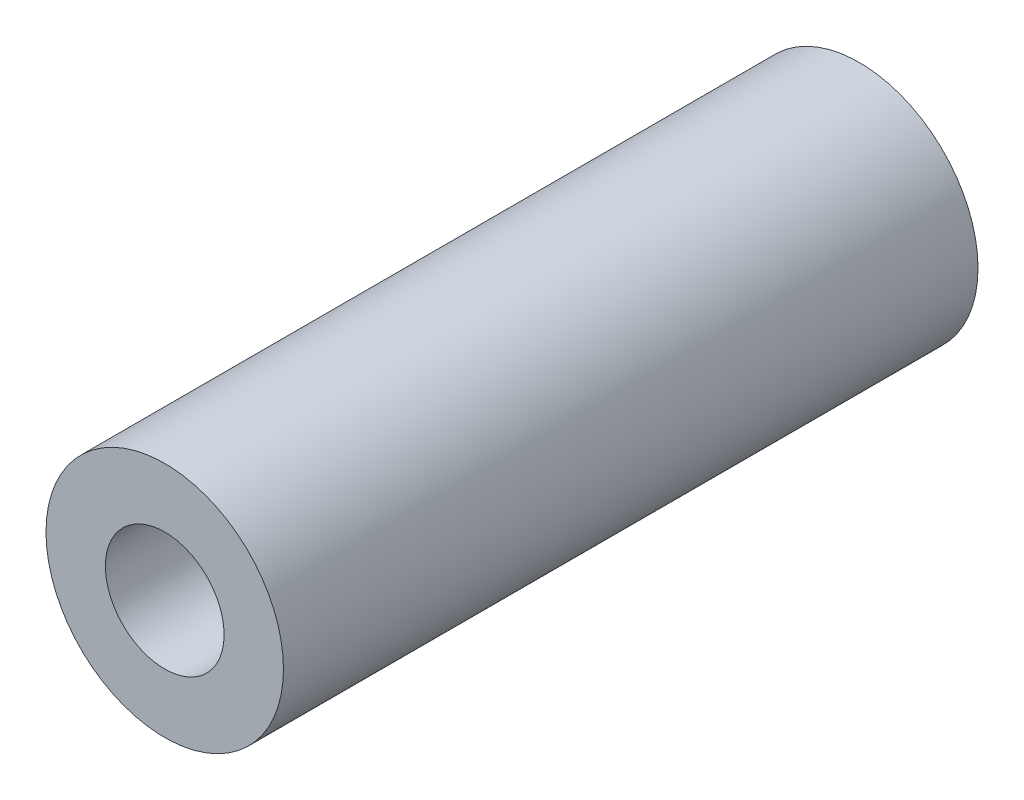
SolidWorks part; units mm, degrees
ref_plane "Alzado" through (0, 0, 0) normal (0, 0, 1) x (1, 0, 0)
ref_plane "Planta" through (0, 0, 0) normal (0, 1, 0) x (1, 0, 0)
ref_plane "Vista lateral" through (0, 0, 0) normal (1, 0, 0) x (0, 0, -1)
sketch "Croquis1" plane through (0, 0, 0) normal (0, 0, 1) x (1, 0, 0)
  circle A0 centre (0, 0) radius 1
  circle A1 centre (0, 0) radius 2
  dimension "D1" = 2
  dimension "D2" = 4
extrude "Saliente-Extruir1" add sketch "Croquis1" against normal up to surface (11.7 mm away)
